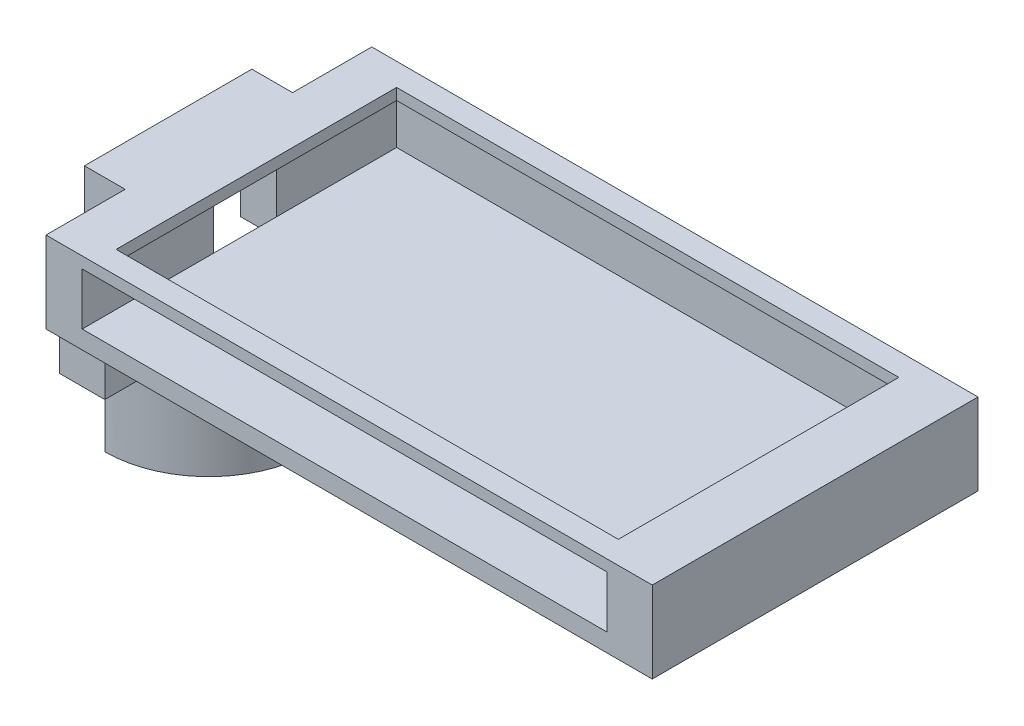
SolidWorks part; units mm, degrees
ref_plane "Front Plane" through (0, 0, 0) normal (0, 0, 1) x (1, 0, 0)
ref_plane "Top Plane" through (0, 0, 0) normal (0, 1, 0) x (1, 0, 0)
ref_plane "Right Plane" through (0, 0, 0) normal (1, 0, 0) x (0, 0, -1)
sketch "Sketch5" plane through (0, 0, 0) normal (0, 1, 0) x (1, 0, 0)
  line L0 (-124, 0) -> (-134, 0)
  line L1 (0, 0) -> (-1.9533, 0)
  line L2 (0, 0) -> (0, 72)
  line L3 (0, 72) -> (-134, 72)
  line L4 (-134, 0) -> (-134, 72)
  line L6 (-10, 2.5) -> (-10, 69.5)
  line L7 (-10, 69.5) -> (-126, 69.5)
  line L8 (-126, 2.5) -> (-126, 69.5)
  line L9 (-126, 2.5) -> (-10, 2.5)
  line L10 (-124, 0) -> (-1.9533, 0)
  dimension "D1" = 72
  dimension "D2" = 134
  dimension "D3" = 116
  dimension "D5" = 10
  dimension "D6" = 2.5
  dimension "D7" = 2.5
extrude "Main Body" add sketch "Sketch5" against normal blind 14 contours L1 L8 L7 L6 L2 L3 L4
sketch "Sketch6" plane through (0, 0, 0) normal (0, 1, 0) x (1, 0, 0)
  line L5 (-10, 2.5) -> (-126, 2.5)
  line L6 (-10, 2.5) -> (-10, 69.5)
  line L7 (-10, 69.5) -> (-126, 69.5)
  line L8 (-126, 2.5) -> (-126, 69.5)
  line L9 (-12.5, 5) -> (-123.5, 5)
  line L10 (-12.5, 5) -> (-12.5, 67)
  line L11 (-12.5, 67) -> (-123.5, 67)
  line L12 (-123.5, 5) -> (-123.5, 67)
  dimension "D1" = 2.5
  dimension "D2" = 2.5
  dimension "D3" = 2.5
  dimension "D4" = 2.5
extrude "Rail" add sketch "Sketch6" against normal blind 2.5
sketch "Sketch8" plane through (0, 0, 0) normal (0, 0, 1) x (1, 0, 0)
  line L0 (-134, -14) -> (-134, 0) construction
  line L1 (0, -14) -> (-134, -14)
  line L2 (0, -14) -> (0, -18)
  line L3 (0, -18) -> (-134, -18)
  line L4 (-134, -14) -> (-134, -18)
  dimension "D1" = 4
extrude "Cover" add sketch "Sketch8" against normal up to surface (72 mm away) up to face at (-67, -7, -72)
sketch "Sketch9" plane through (-134, 0, 0) normal (-1, 0, 0) x (0, 0, 1)
  line L0 (-72, -18) -> (0, -18) construction
  line L1 (-29, -18) -> (-43, -18)
  line L2 (-29, -18) -> (-29, -4)
  line L3 (-29, -4) -> (-43, -4)
  line L4 (-43, -18) -> (-43, -4)
  line L5 (-72, -18) -> (-72, 0) construction
  dimension "D1" = 14
  dimension "D2" = 14
  dimension "D3" = 29
extrude "SiPM Window" cut sketch "Sketch9" against normal up to surface (8 mm away) up to face at (-126, -8.25, -36)
sketch "Sketch10" plane through (0, -18, 0) normal (0, -1, 0) x (1, 0, 0)
  line L0 (-134, -72) -> (-134, -43) construction
  line L4 (-134, -29) -> (-134, 0) construction
  line L5 (-134, -72) -> (0, -72) construction
  line L6 (-134, -16) -> (-134, -13)
  line L7 (-134, -56) -> (-134, -59)
  arc A0 (-134, -56) -> (-134, -16) centre (-134, -36) ccw
  arc A1 (-134, -59) -> (-134, -13) centre (-134, -36) ccw
  line M4 (-134, -43) -> (-134, -72)
  line M8 (-134, 0) -> (-134, -29)
  dimension "D2" = 20
  dimension "D1" = 36
  dimension "D3" = 3
  dimension "D4" = 3
extrude "Tube Adapter" add sketch "Sketch10" along normal blind 30 contours A1 A0 M4 M8
sketch "Sketch11" plane through (0, -18, 0) normal (0, -1, 0) x (1, 0, 0)
  line L0 (-134, -59) -> (-134, -69)
  line L5 (-134, -72) -> (-134, -59) construction
  line L6 (-134, -69) -> (-124, -69)
  line L7 (-124, -69) -> (-124, -56.7123)
  arc A0 (-134, -59) -> (-124, -56.7123) centre (-134, -36) ccw
  dimension "D1" = 10
  dimension "D2" = 10
extrude "Right Screw Terminal" add sketch "Sketch11" along normal blind 10
sketch "Sketch12" plane through (-134, 0, 0) normal (-1, 0, 0) x (0, 0, 1)
  line L2 (-69, -28) -> (-69, -18) construction
  line L3 (-59, -28) -> (-69, -28) construction
  circle A0 centre (-64, -23) radius 1.524
  dimension "D3" = 5
  dimension "D1" = 3.048
  dimension "D2" = 5
extrude "Right Screw Hole" cut sketch "Sketch12" against normal up to next
sketch "Sketch13" plane through (0, -18, 0) normal (0, -1, 0) x (-1, 0, 0)
  line L2 (134, 13) -> (134, 3)
  line L3 (134, 3) -> (124, 3)
  line L4 (124, 15.2877) -> (124, 3)
  arc A0 (134, 13) -> (124, 15.2877) centre (134, 36) cw
  dimension "D1" = 10
  dimension "D2" = 10
extrude "Left Screw Terminal" add sketch "Sketch13" along normal blind 10
sketch "Sketch14" plane through (-134, 0, 0) normal (-1, 0, 0) x (0, 0, 1)
  line L0 (-3, -28) -> (-3, -18) construction
  line L1 (-3, -28) -> (-13, -28) construction
  circle A0 centre (-8, -23) radius 1.524
  dimension "D3" = 3.048
  dimension "D1" = 5
  dimension "D2" = 5
extrude "Left Screw Hole" cut sketch "Sketch14" against normal up to next
sketch "Sketch15" plane through (-134, 0, 0) normal (-1, 0, 0) x (0, 0, 1)
  line L0 (-29, -18) -> (-16, -18) construction
  line L1 (-17.5, -18) -> (-54.5, -18)
  line L2 (-17.5, -18) -> (-17.5, 0)
  line L3 (-17.5, 0) -> (-54.5, 0)
  line L4 (-54.5, -18) -> (-54.5, 0)
  line L7 (0, 0) -> (-72, 0) construction
  line L8 (-43, -4) -> (-43, -18) construction
  dimension "D1" = 37
  dimension "D2" = 11.5
extrude "SiPM Mount" add sketch "Sketch15" along normal blind 9
sketch "Sketch17" plane through (0, -18, 0) normal (0, -1, 0) x (1, 0, 0)
  line L0 (-126, -29) -> (-134, -29) construction
  line L1 (-134, -18) -> (-142.8, -18)
  line L2 (-134, -18) -> (-134, -54)
  line L3 (-134, -54) -> (-142.8, -54)
  line L4 (-142.8, -18) -> (-142.8, -54)
  line L5 (-134, -43) -> (-134, -29) construction
  dimension "D1" = 36
  dimension "D2" = 11
  dimension "D3" = 8.8
extrude "Cut-Extrude1" cut sketch "Sketch17" against normal offset from surface (16 mm away) 2 up to face at (-102.75, 0, -36)
ref_plane "Plane1" through (-144, 0, 0) normal (-1, 0, 0) x (0, 0, 1)
sketch "Sketch18" plane through (-144, 0, 0) normal (-1, 0, 0) x (0, 0, 1)
  line L3 (-56, -48) -> (-56, -18) construction
  line L5 (-56, -48) -> (-16, -48) construction
  circle A0 centre (-36, -40.5) radius 1.524
  dimension "D1" = 3.048
  dimension "D2" = 20
  dimension "D3" = 7.5
extrude "Adapter Hole" cut sketch "Sketch18" against normal up to surface (32.9495 mm away)
sketch "Sketch19" plane through (0, 0, -2.5) normal (0, 0, -1) x (-1, 0, 0)
  line L0 (126, -14) -> (126, -2.5) construction
  line L1 (10, -14) -> (126, -14)
  line L2 (10, -14) -> (10, -2.5)
  line L3 (10, -2.5) -> (126, -2.5)
  line L4 (126, -14) -> (126, -2.5)
extrude "Cut-Extrude2" cut sketch "Sketch19" against normal blind 10
